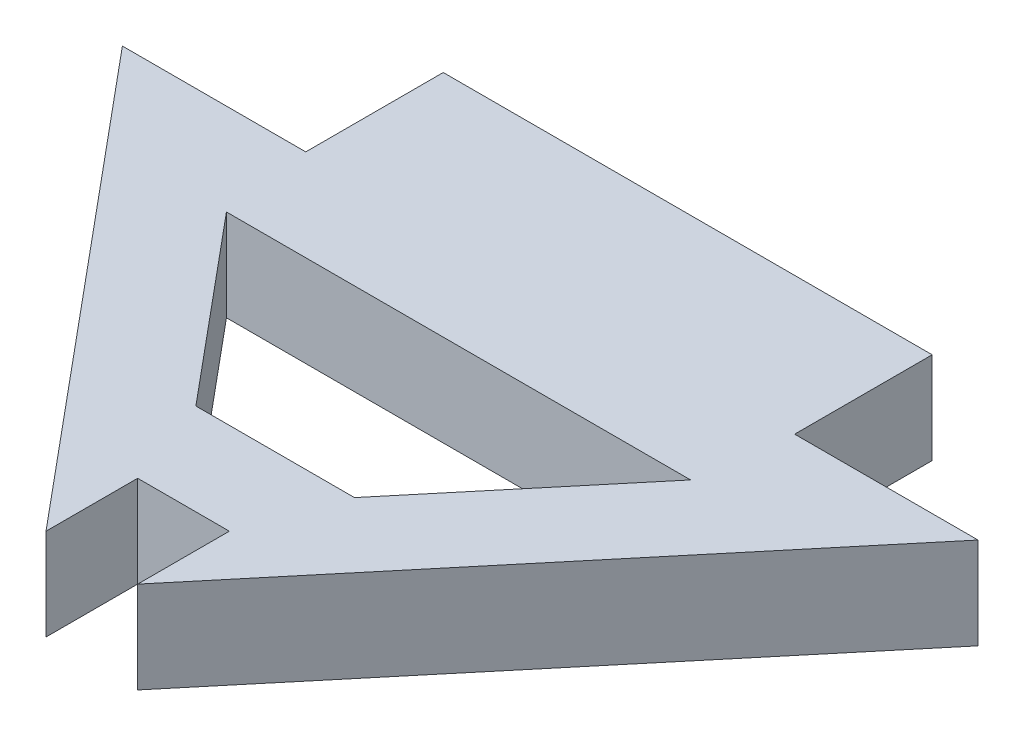
SolidWorks part; units mm, degrees
material "Custom Plastic"
ref_plane "Front Plane" through (0, 0, 0) normal (0, 0, 1) x (1, 0, 0)
ref_plane "Top Plane" through (0, 0, 0) normal (0, 1, 0) x (1, 0, 0)
ref_plane "Right Plane" through (0, 0, 0) normal (1, 0, 0) x (0, 0, -1)
sketch "Sketch1" plane through (0, 0, 0) normal (0, 1, 0) x (1, 0, 0)
  line L0 (22.0795, 3.0287) -> (16.0795, 3.0287)
  line L1 (16.0795, 3.0287) -> (16.0795, 7.5287)
  line L2 (16.0795, 7.5287) -> (0.0795, 7.5287)
  line L3 (0.0795, 7.5287) -> (0.0795, 3.0287)
  line L4 (0.0795, 3.0287) -> (-5.9205, 3.0287)
  line L5 (-5.9205, 3.0287) -> (6.5795, -11.9713)
  line L6 (6.5795, -11.9713) -> (6.5795, -8.9713)
  line L7 (6.5795, -8.9713) -> (9.5795, -8.9713)
  line L8 (9.5795, -8.9713) -> (9.5795, -11.9713)
  line L9 (9.5795, -11.9713) -> (22.0795, 3.0287)
  line L10 (8.0795, 7.5287) -> (8.0795, -8.9713) construction
  line L11 (9.5795, -11.9713) -> (6.5795, -11.9713) construction
  line L12 (15.6744, 0.0287) -> (0.4846, 0.0287)
  line L13 (0.4846, 0.0287) -> (5.4846, -5.9713)
  line L14 (5.4846, -5.9713) -> (10.6744, -5.9713)
  line L15 (10.6744, -5.9713) -> (15.6744, 0.0287)
  point P12 (6.5795, -10.4713)
  dimension "D1" = 3
  dimension "D2" = 28
  dimension "D3" = 4.5
  dimension "D4" = 6
  dimension "D5" = 12
  dimension "D6" = 3
  dimension "D7" = 3
  dimension "D8" = 3
  dimension "D9" = 3
  dimension "D10" = 3
extrude "Boss-Extrude1" add sketch "Sketch1" along normal blind 3
